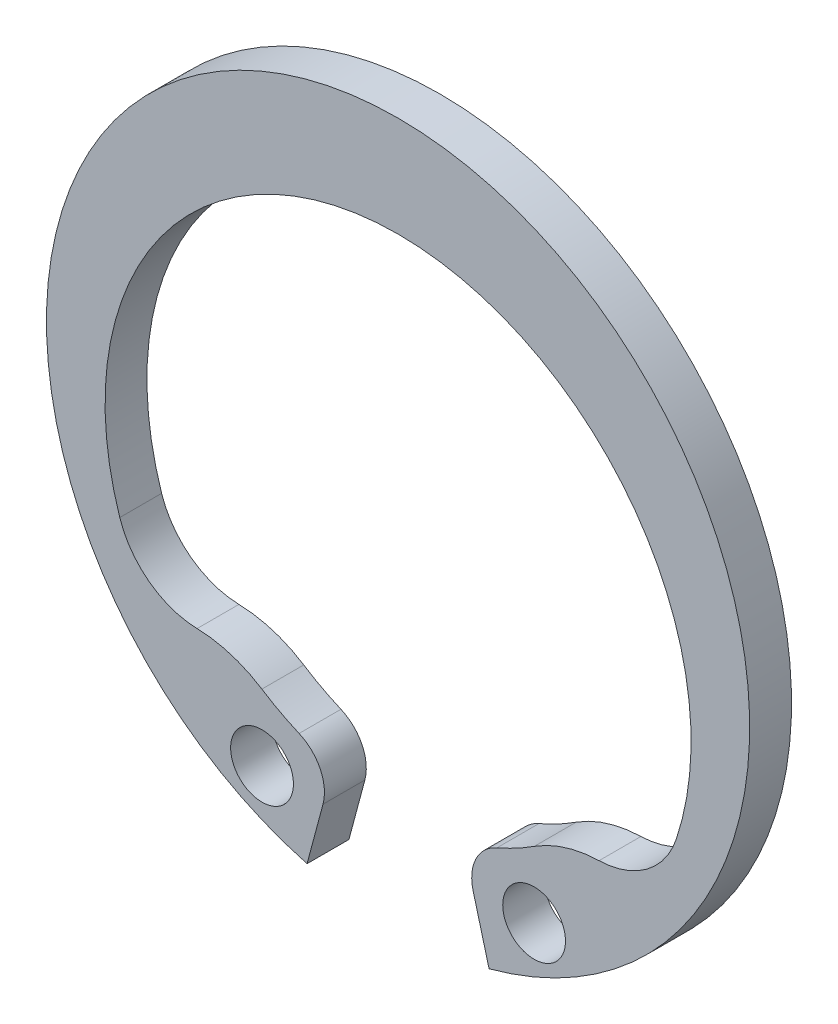
SolidWorks part; units mm, degrees
ref_plane "Plane1" through (0, 0, 0) normal (0, 0, 1) x (1, 0, 0)
ref_plane "Plane2" through (0, 0, 0) normal (0, 1, 0) x (1, 0, 0)
ref_plane "Plane3" through (0, 0, 0) normal (1, 0, 0) x (0, 0, -1)
sketch "Esquisse1" plane through (0, 0, 0) normal (0, 0, 1) x (1, 0, 0)
  line L0 (0, 0) -> (50, 0) construction
  line L1 (0, 0) -> (0, 60) construction
  line L2 (-2.1741, -8.1138) -> (-1.7932, -6.6921)
  line L3 (0, 6) -> (0, 8.4)
  arc A0 (-2.1741, -8.1138) -> (0, 8.4) centre (0, 0) cw
  arc A1 (-6.649, -3.1888) -> (0, 6) centre (0, -1) cw
  arc A2 (-2.3649, -5.5143) -> (-3.2538, -5.0411) centre (0, 0) cw
  arc A3 (-2.3649, -5.5143) -> (-1.7932, -6.6921) centre (-2.7591, -6.4333) cw
  arc A4 (-6.649, -3.1888) -> (-4.8018, -4.5627) centre (-4.7493, -2.5634) ccw
  arc A5 (-4.8018, -4.5627) -> (-3.2538, -5.0411) centre (-4.8807, -7.5617) cw
  dimension "D1" = 8.4
  dimension "D3" = 7
  dimension "D5" = 6
  dimension "D6" = 1
  dimension "D7" = 3
  dimension "D8" = 2
  dimension "D2" = 15
  dimension "D4" = 1
extrude "Base-Extrusion" add sketch "Esquisse1" along normal blind 1
mirror "Symétrie1"
sketch "Esquisse2" plane through (0, 0, 1) normal (0, 0, 1) x (1, 0, 0)
  line L0 (0, -1) -> (0, -11.8465) construction
  line L1 (-3.25, -6.6292) -> (0, -1) construction
  circle A0 centre (-3.25, -6.6292) radius 0.75
  dimension "D2" = 1.5
  dimension "D1" = 30
  dimension "D3" = 6.5
extrude "Enlèv. mat.-Extru.1" cut sketch "Esquisse2" against normal through all
mirror "Symétrie2" about plane through (0, 0, 0) normal (1, 0, 0)
